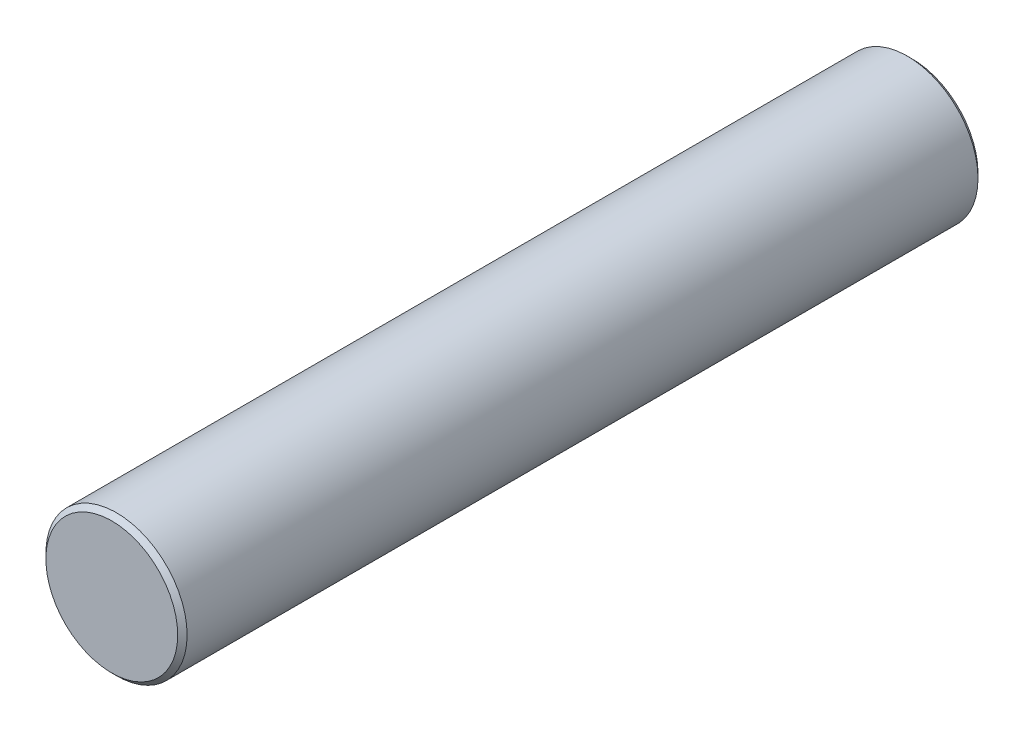
SolidWorks part; units mm, degrees
ref_plane "Face" through (0, 0, 0) normal (0, 0, 1) x (1, 0, 0)
ref_plane "Dessus" through (0, 0, 0) normal (0, 1, 0) x (1, 0, 0)
ref_plane "Droite" through (0, 0, 0) normal (1, 0, 0) x (0, 0, -1)
sketch "Esquisse1" plane through (0, 0, 0) normal (0, 0, 1) x (1, 0, 0)
  circle A0 centre (0, 0) radius 15
  dimension "D1" = 30
extrude "Extrusion1" add sketch "Esquisse1" along normal blind 170
chamfer "Chanfrein1" distance 1 angle 45 2 edges at (15, 0, 0) (15, 0, 170)
